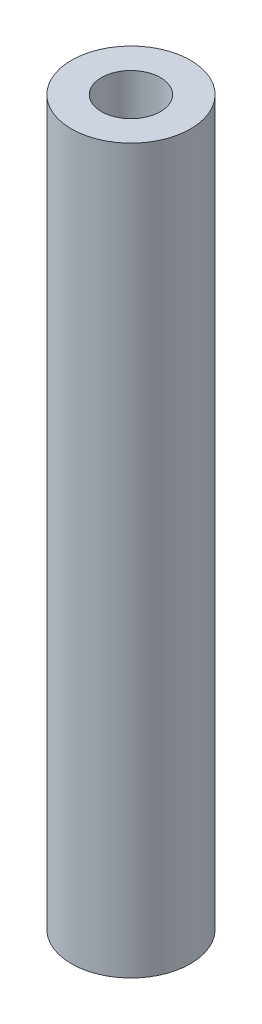
SolidWorks part; units mm, degrees
ref_plane "Front Plane" through (0, 0, 0) normal (0, 0, 1) x (1, 0, 0)
ref_plane "Top Plane" through (0, 0, 0) normal (0, 1, 0) x (1, 0, 0)
ref_plane "Right Plane" through (0, 0, 0) normal (1, 0, 0) x (0, 0, -1)
sketch "Sketch1" plane through (0, 0, 0) normal (0, 1, 0) x (1, 0, 0)
  circle A0 centre (0, 0) radius 25.5083
  circle A1 centre (0, 0) radius 12.6518
extrude "Boss-Extrude1" add sketch "Sketch1" along normal blind 309.88
